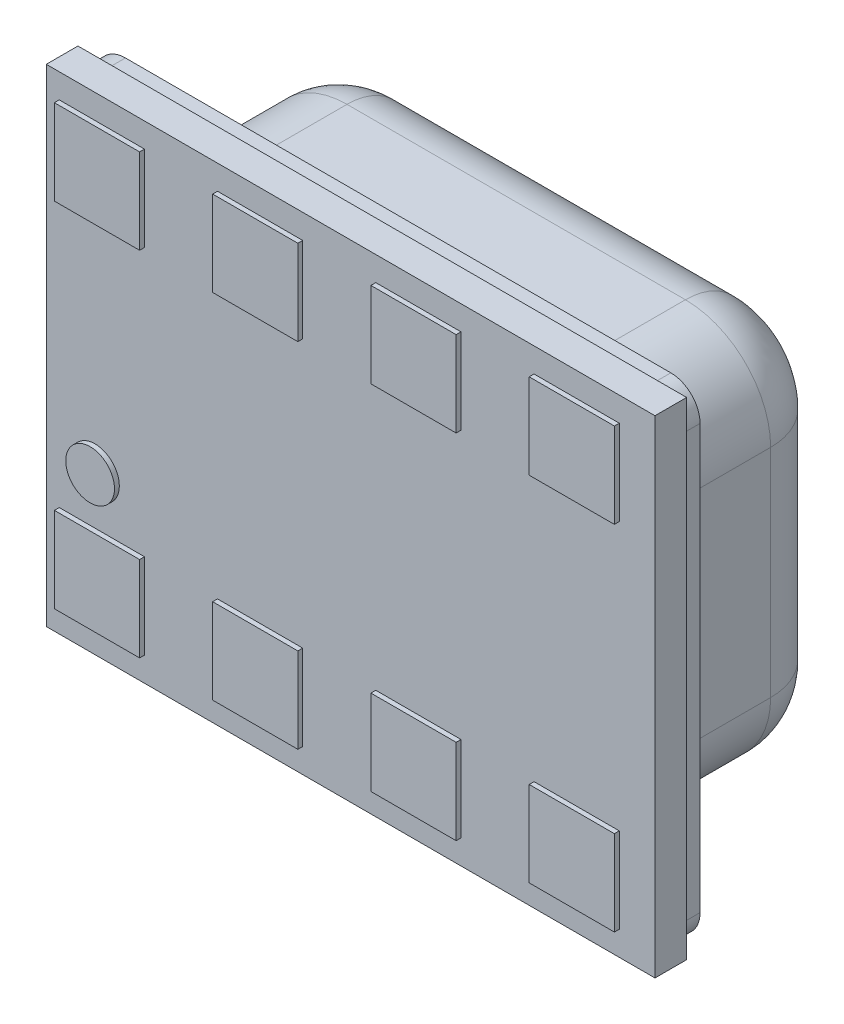
SolidWorks part; units mm, degrees
ref_plane "Спереди" through (0, 0, 0) normal (0, 0, 1) x (1, 0, 0)
ref_plane "Сверху" through (0, 0, 0) normal (0, 1, 0) x (1, 0, 0)
ref_plane "Справа" through (0, 0, 0) normal (1, 0, 0) x (0, 0, -1)
sketch "Эскиз1" plane through (0, 0, 0) normal (0, 0, -1) x (1, 0, 0)
  line L1 (0, 0) -> (2.5, 0)
  line L2 (0, 0) -> (0, 2)
  line L3 (0, 2) -> (2.5, 2)
  line L4 (2.5, 0) -> (2.5, 2)
  dimension "D1" = 2
  dimension "D2" = 2.5
extrude "Бобышка-Вытянуть1" add sketch "Эскиз1" along normal blind 0.13
sketch "Эскиз2" plane through (0, 0, -0.13) normal (0, 0, -1) x (1, 0, 0)
  line L0 (1.25, 2) -> (1.25, 0) construction
  line L5 (2.5, 2) -> (0, 2) construction
  line L6 (0, 0) -> (2.5, 0) construction
  line L7 (0, 1) -> (2.5, 1) construction
  line L8 (0, 2) -> (0, 0) construction
  line L9 (2.5, 0) -> (2.5, 2) construction
  line L11 (0.13, 0.01) -> (2.37, 0.01)
  line L12 (0.01, 0.13) -> (0.01, 1.87)
  line L13 (0.13, 1.99) -> (2.37, 1.99)
  line L14 (2.49, 0.13) -> (2.49, 1.87)
  line L15 (0.01, 0.01) -> (2.49, 1.99) construction
  line L16 (0.01, 1.99) -> (2.49, 0.01) construction
  arc A0 (0.13, 0.01) -> (0.01, 0.13) centre (0.13, 0.13) cw
  arc A1 (2.37, 0.01) -> (2.49, 0.13) centre (2.37, 0.13) ccw
  arc A2 (2.37, 1.99) -> (2.49, 1.87) centre (2.37, 1.87) cw
  arc A3 (0.01, 1.87) -> (0.13, 1.99) centre (0.13, 1.87) cw
  point P12 (1.25, 1)
  dimension "D3" = 0.12
  dimension "D1" = 2.48
  dimension "D2" = 1.98
extrude "Бобышка-Вытянуть2" add sketch "Эскиз2" along normal blind 0.065
sketch "Эскиз3" plane through (0, 0, -0.195) normal (0, 0, -1) x (1, 0, 0)
  line L0 (1.25, 1.99) -> (1.25, 0.01) construction
  line L1 (2.37, 1.99) -> (0.13, 1.99) construction
  line L2 (0.13, 0.01) -> (2.37, 0.01) construction
  line L3 (0.01, 1) -> (2.49, 1) construction
  line L4 (0.01, 1.87) -> (0.01, 0.13) construction
  line L5 (2.49, 0.13) -> (2.49, 1.87) construction
  line L7 (0.555, 0.205) -> (1.945, 0.205)
  line L8 (0.205, 0.555) -> (0.205, 1.445)
  line L9 (0.555, 1.795) -> (1.945, 1.795)
  line L10 (2.295, 0.555) -> (2.295, 1.445)
  line L11 (0.205, 0.205) -> (2.295, 1.795) construction
  line L12 (0.205, 1.795) -> (2.295, 0.205) construction
  arc A0 (0.555, 0.205) -> (0.205, 0.555) centre (0.555, 0.555) cw
  arc A1 (1.945, 0.205) -> (2.295, 0.555) centre (1.945, 0.555) ccw
  arc A2 (1.945, 1.795) -> (2.295, 1.445) centre (1.945, 1.445) cw
  arc A3 (0.205, 1.445) -> (0.555, 1.795) centre (0.555, 1.445) cw
  point P12 (1.25, 1)
  dimension "D3" = 0.35
  dimension "D1" = 1.59
  dimension "D2" = 2.09
extrude "Бобышка-Вытянуть3" add sketch "Эскиз3" along normal blind 0.755
fillet "Скругление1" radius 0.1 8 edges at (1.25, -1.795, -0.195) (0.205, -1, -0.195) (1.25, -0.205, -0.195) (2.295, -1, -0.195) (2.1925, -0.3075, -0.195) (0.3075, -0.3075, -0.195) (0.3075, -1.6925, -0.195) (2.1925, -1.6925, -0.195)
fillet "Скругление2" radius 0.27 8 edges at (0.205, -1, -0.95) (0.3075, -1.6925, -0.95) (1.25, -1.795, -0.95) (2.1925, -1.6925, -0.95) (2.295, -1, -0.95) (2.1925, -0.3075, -0.95) (1.25, -0.205, -0.95) (0.3075, -0.3075, -0.95)
sketch "Эскиз4" plane through (0, 0, -0.13) normal (0, 0, -1) x (1, 0, 0)
  line L0 (0, 1) -> (2.49, 1) construction
  line L1 (0.65, 0.3) -> (1.85, 0.3)
  line L2 (0.3, 0.65) -> (0.3, 1.35)
  line L3 (0.65, 1.7) -> (1.85, 1.7)
  line L4 (2.2, 0.65) -> (2.2, 1.35)
  line L5 (0.3, 0.3) -> (2.2, 1.7) construction
  line L6 (0.3, 1.7) -> (2.2, 0.3) construction
  line L7 (0, 2) -> (0, 0) construction
  line L8 (2.49, 0.13) -> (2.49, 1.87) construction
  line L9 (1.25, 2) -> (1.25, 0) construction
  line L10 (2.5, 2) -> (0, 2) construction
  line L11 (0, 0) -> (2.5, 0) construction
  arc A0 (0.65, 0.3) -> (0.3, 0.65) centre (0.65, 0.65) cw
  arc A1 (1.85, 0.3) -> (2.2, 0.65) centre (1.85, 0.65) ccw
  arc A2 (1.85, 1.7) -> (2.2, 1.35) centre (1.85, 1.35) cw
  arc A3 (0.3, 1.35) -> (0.65, 1.7) centre (0.65, 1.35) cw
  point P0 (1.25, 1)
  dimension "D3" = 0.35
  dimension "D1" = 1.4
  dimension "D2" = 1.9
extrude "Вырез-Вытянуть1" cut sketch "Эскиз4" along normal blind 0.75
fillet "Скругление3" radius 0.2 8 edges at (1.25, -0.3, -0.88) (2.0975, -0.4025, -0.88) (2.2, -1, -0.88) (2.0975, -1.5975, -0.88) (1.25, -1.7, -0.88) (0.4025, -1.5975, -0.88) (0.3, -1, -0.88) (0.4025, -0.4025, -0.88)
sketch "Эскиз5" plane through (0, 0, -0.13) normal (0, 0, -1) x (1, 0, 0)
  line L0 (1.25, 2) -> (1.25, 0) construction
  line L1 (2.5, 2) -> (0, 2) construction
  line L2 (0, 0) -> (2.5, 0) construction
  line L3 (0, 1) -> (2.5, 1) construction
  line L4 (0, 2) -> (0, 0) construction
  line L5 (2.5, 0) -> (2.5, 2) construction
  line L7 (0.6, 0.5) -> (1.9, 0.5)
  line L8 (0.6, 0.5) -> (0.6, 1.5)
  line L9 (0.6, 1.5) -> (1.9, 1.5)
  line L10 (1.9, 0.5) -> (1.9, 1.5)
  line L11 (0.6, 0.5) -> (1.9, 1.5) construction
  line L12 (0.6, 1.5) -> (1.9, 0.5) construction
  point P12 (1.25, 1)
  dimension "D1" = 1.3
  dimension "D2" = 1
extrude "Бобышка-Вытянуть4" add sketch "Эскиз5" along normal blind 0.3
sketch "Эскиз6" plane through (0, 0, -0.95) normal (0, 0, -1) x (1, 0, 0)
  line L0 (-0.1672, 1.175) -> (1.6013, 1.175) construction
  line L1 (0.825, 2.056) -> (0.825, 0.7542) construction
  line L2 (0, 2) -> (0, 0) construction
  line L3 (2.5, 2) -> (0, 2) construction
  circle A0 centre (0.825, 1.175) radius 0.15
  dimension "D3" = 0.3
  dimension "D1" = 0.825
  dimension "D2" = 0.825
extrude "Вырез-Вытянуть2" cut sketch "Эскиз6" against normal blind 0.1
sketch "Эскиз7" plane through (0, 0, -0.95) normal (0, 0, -1) x (1, 0, 0)
  line L0 (1.8844, 0.8044) -> (0.475, 0.8044) construction
  line L2 (0.475, 1.445) -> (0.475, 0.555) construction
  text T0 "BMP280" font "Kozuka Mincho Pr6N R" height 0.25
extrude "Вырез-Вытянуть3" cut sketch "Эскиз7" against normal blind 0.02
sketch "Эскиз8" plane through (0, -0.95, -0.95) normal (0, 0, 1) x (1, 0, 0)
  line L0 (1.5814, -0.0728) -> (1.5814, -0.1521)
  line L1 (1.5814, -0.1521) -> (1.7267, -0.1521)
  line L2 (1.8702, 0.1578) -> (1.8702, 0.146) construction
  line L3 (-15.1264, -250.2991) -> (-18.3554, -250.2991)
  line L4 (-18.3554, -250.2991) -> (-18.3554, -252.0185)
  line L5 (-18.3554, -252.0185) -> (-15.1264, -252.0185)
  line L7 (1.7267, -0.3014) -> (1.5814, -0.3014)
  line L8 (1.5814, -0.3014) -> (1.5814, -0.3807)
  line L9 (1.5479, -0.1365) -> (1.5479, -0.317)
  line L10 (1.7602, -0.1365) -> (1.7602, -0.317)
  line L11 (1.7267, -0.3014) -> (1.7267, -0.3807)
  line L12 (-15.1264, -250.2991) -> (-15.1264, -252.0185)
  line L13 (1.7267, -0.0728) -> (1.7267, -0.1521)
  line L14 (1.654, -0.0666) -> (1.654, -0.6316) construction
  line L15 (2.0503, -0.2308) -> (1.1116, -0.2308) construction
  circle A0 centre (1.654, -0.2268) radius 0.252
  circle A1 centre (1.654, -0.2268) radius 0.207
  arc A2 (1.5715, -0.0668) -> (1.5715, -0.3867) centre (1.654, -0.2268) ccw
  arc A3 (1.5479, -0.1365) -> (1.5479, -0.317) centre (1.654, -0.2268) ccw
  arc A4 (1.5715, -0.3867) -> (1.5814, -0.3807) centre (1.5746, -0.3807) ccw
  arc A5 (1.5814, -0.0728) -> (1.5715, -0.0668) centre (1.5746, -0.0728) ccw
  arc A6 (1.7267, -0.0728) -> (1.7365, -0.0668) centre (1.7334, -0.0728) cw
  arc A7 (1.7365, -0.3867) -> (1.7267, -0.3807) centre (1.7334, -0.3807) cw
  arc A8 (1.7602, -0.1365) -> (1.7602, -0.317) centre (1.654, -0.2268) cw
  arc A9 (1.7365, -0.0668) -> (1.7365, -0.3867) centre (1.654, -0.2268) cw
  point P34 (-15.1264, -247.4991)
  dimension "D3" = 0.18
  dimension "D9" = 0.0271
  dimension "D15" = 0.0267
extrude "Вырез-Вытянуть7" cut sketch "Эскиз8" along direction (0, 0, 1) on the side of the normal blind 0.02 contours A6 A9 A7 L11 L7 L8 A4 A2 A5 L0 L1 L13 L9 A3 A8 L10 | A0 A1
sketch "Эскиз10" plane through (0, 0, 0) normal (0, 0, 1) x (1, 0, 0)
  line L0 (-0.4102, -1.35) -> (2.7056, -1.35) construction
  line L1 (0.2, -2.2653) -> (0.2, 0.1314) construction
  line L2 (1.0532, -1.9) -> (1.0532, -1.55)
  line L3 (0.0532, -1.9) -> (0.4032, -1.9)
  line L4 (-0.2161, -0.1535) -> (2.7056, -0.1535) construction
  line L5 (2.5, -2) -> (0, -2) construction
  line L6 (0, -2) -> (0, 0) construction
  line L7 (0.0532, -1.9) -> (0.0532, -1.55)
  line L8 (0.0532, -1.55) -> (0.4032, -1.55)
  line L9 (0.4032, -1.9) -> (0.4032, -1.55)
  line L10 (0.0532, -1.9) -> (0.4032, -1.55) construction
  line L11 (0.0532, -1.55) -> (0.4032, -1.9) construction
  line L12 (0.7032, -1.9) -> (1.0532, -1.9)
  line L13 (0.7032, -1.9) -> (0.7032, -1.55)
  line L14 (0.7032, -1.55) -> (1.0532, -1.55)
  line L15 (1.7032, -1.9) -> (1.7032, -1.55)
  line L16 (1.3532, -1.9) -> (1.7032, -1.9)
  line L17 (1.3532, -1.9) -> (1.3532, -1.55)
  line L18 (1.3532, -1.55) -> (1.7032, -1.55)
  line L19 (2.3532, -1.9) -> (2.3532, -1.55)
  line L20 (2.0032, -1.9) -> (2.3532, -1.9)
  line L21 (2.0032, -1.9) -> (2.0032, -1.55)
  line L22 (2.0032, -1.55) -> (2.3532, -1.55)
  line L23 (1.0532, -0.45) -> (1.0532, -0.1)
  line L24 (0.7032, -0.45) -> (1.0532, -0.45)
  line L25 (0.7032, -0.45) -> (0.7032, -0.1)
  line L26 (0.7032, -0.1) -> (1.0532, -0.1)
  line L27 (1.7032, -0.45) -> (1.7032, -0.1)
  line L28 (1.3532, -0.45) -> (1.7032, -0.45)
  line L29 (1.3532, -0.45) -> (1.3532, -0.1)
  line L30 (1.3532, -0.1) -> (1.7032, -0.1)
  line L31 (2.3532, -0.45) -> (2.3532, -0.1)
  line L32 (2.0032, -0.45) -> (2.3532, -0.45)
  line L33 (2.0032, -0.45) -> (2.0032, -0.1)
  line L34 (2.0032, -0.1) -> (2.3532, -0.1)
  line L35 (0.4032, -0.45) -> (0.4032, -0.1)
  line L36 (0.0532, -0.45) -> (0.4032, -0.45)
  line L37 (0.0532, -0.45) -> (0.0532, -0.1)
  line L38 (0.0532, -0.1) -> (0.4032, -0.1)
  circle A0 centre (0.2, -1.35) radius 0.1
  point P6 (0.2282, -1.725)
  point P16 (0, -1)
  dimension "D1" = 0.2
  dimension "D2" = 0.65
  dimension "D3" = 0.2
  dimension "D4" = 0.35
  dimension "D5" = 0.35
  dimension "D6" = 0.55
  dimension "D7" = 4
  dimension "D8" = 2
extrude "Бобышка-Вытянуть5" add sketch "Эскиз10" along normal blind 0.02
